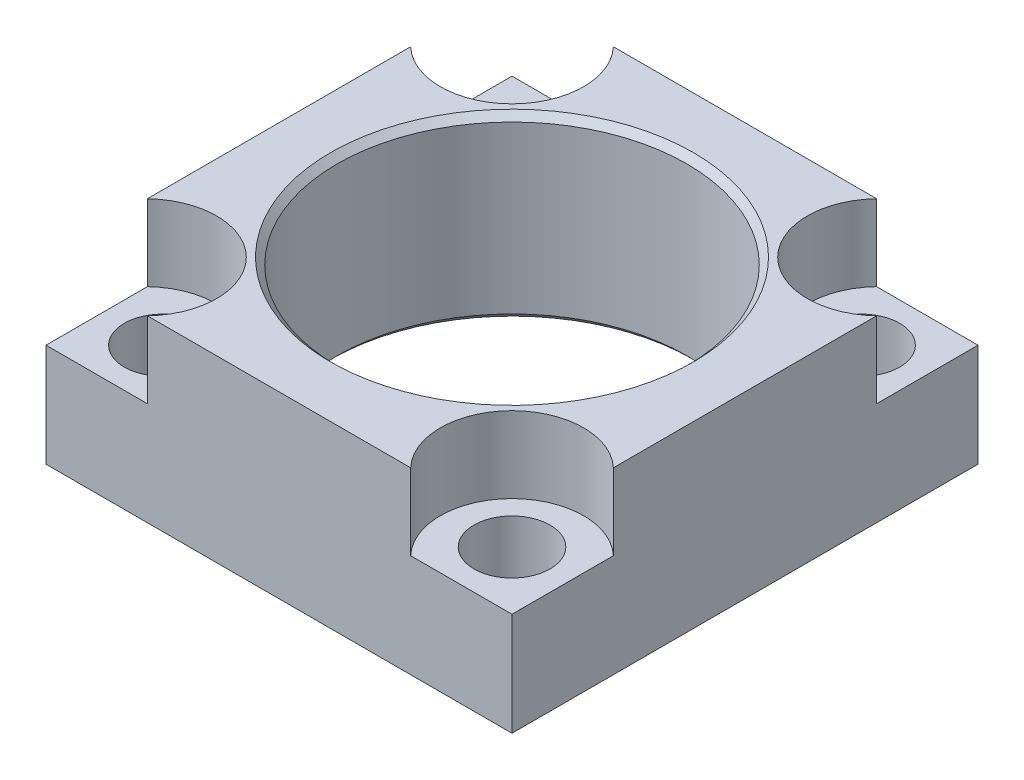
SolidWorks part; units mm, degrees
material "Alloy Steel"
ref_plane "Front Plane" through (0, 0, 0) normal (0, 0, 1) x (1, 0, 0)
ref_plane "Top Plane" through (0, 0, 0) normal (0, 1, 0) x (1, 0, 0)
ref_plane "Right Plane" through (0, 0, 0) normal (1, 0, 0) x (0, 0, -1)
sketch "Sketch1" plane through (0, 0, 0) normal (0, 1, 0) x (1, 0, 0)
  line L0 (41.275, 41.275) -> (-41.275, -41.275) construction
  line L1 (-41.275, 41.275) -> (41.275, 41.275)
  line L2 (-41.275, 41.275) -> (-41.275, -41.275)
  line L3 (-41.275, -41.275) -> (41.275, -41.275)
  line L4 (41.275, 41.275) -> (41.275, -41.275)
  line L5 (-41.275, 41.275) -> (41.275, -41.275) construction
  circle A0 centre (0, 0) radius 30.9753
  dimension "D3" = 61.9506
  dimension "D1" = 82.55
  dimension "D2" = 82.55
extrude "Extrude1" add sketch "Sketch1" along normal blind 31.75
sketch "Sketch2" plane through (0, 31.75, 0) normal (0, 1, 0) x (1, 0, 0)
  line L0 (-41.275, -41.275) -> (41.275, -41.275) construction
  line L1 (41.275, -41.275) -> (41.275, 41.275) construction
  line L2 (23.3196, -41.275) -> (41.275, -41.275)
  line L3 (41.275, -41.275) -> (41.275, -23.3196)
  line L4 (0, 0) -> (-25.3528, 0) construction
  line L5 (0, 0) -> (0, 27.5861) construction
  line L6 (41.275, 41.275) -> (41.275, 23.3196)
  line L7 (23.3196, 41.275) -> (41.275, 41.275)
  line L8 (-23.3196, 41.275) -> (-41.275, 41.275)
  line L9 (-41.275, 41.275) -> (-41.275, 23.3196)
  line L10 (-41.275, -41.275) -> (-41.275, -23.3196)
  line L11 (-23.3196, -41.275) -> (-41.275, -41.275)
  arc A0 (41.275, -23.3196) -> (23.3196, -41.275) centre (32.512, -32.512) ccw
  arc A1 (41.275, 23.3196) -> (23.3196, 41.275) centre (32.512, 32.512) cw
  arc A2 (-41.275, 23.3196) -> (-23.3196, 41.275) centre (-32.512, 32.512) ccw
  arc A3 (-41.275, -23.3196) -> (-23.3196, -41.275) centre (-32.512, -32.512) cw
  dimension "D1" = 12.7
  dimension "D2" = 32.512
  dimension "D3" = 32.512
extrude "Cut-Extrude1" cut sketch "Sketch2" against normal blind 13.4874
hole_wizard "Hole1" positions "Sketch4" profile "Sketch3" legacy end condition up to next
sketch "Sketch4" plane through (0, 18.2626, 0) normal (0, 1, 0) x (-1, 0, 0)
  point P0 (30.9626, 30.9626)
  point P6 (30.9626, -30.9626)
  point P9 (-30.9626, 30.9626)
  point P11 (-30.9626, -30.9626)
  dimension "D1" = 30.9626
  dimension "D2" = 30.9626
  dimension "D3" = 61.9252
  dimension "D4" = 61.9252
sketch "Sketch3" plane through (-30.9626, 18.2626, 30.9626) normal (1, 0, 0) x (0, 0, 1)
  line L0 (0, 0) -> (0, 18.2626)
  line L1 (0, 18.2626) -> (6.7437, 18.2626)
  line L2 (6.7437, 18.2626) -> (6.7437, 0)
  line L3 (6.7437, 0) -> (0, 0)
  line L4 (0, 110) -> (0, -10) construction
  dimension "Diameter" = 13.4874
  dimension "Depth" = 18.2626
sketch "Sketch5" plane through (0, 0, 0) normal (1, 0, 0) x (0, 0, -1)
  line L0 (0, 0) -> (0, 13.7269) construction
  line L1 (-22.3145, 15.875) -> (-9.8575, 15.875) construction
  line L2 (-19.812, 31.75) -> (-41.275, 31.75) construction
  line L3 (-41.275, 0) -> (41.275, 0) construction
  line L4 (-32.131, 31.75) -> (-30.9753, 31.75)
  line L5 (-30.9753, 31.75) -> (-30.9753, 30.5943)
  line L6 (-30.9753, 31.75) -> (-30.9753, 0) construction
  line L7 (-30.9753, 30.5943) -> (-32.131, 31.75)
  line L8 (-30.9753, 1.1557) -> (-32.131, 0)
  line L9 (-30.9753, 0) -> (-30.9753, 1.1557)
  line L10 (-32.131, 0) -> (-30.9753, 0)
  dimension "D1" = 45
  dimension "D2" = 64.262
revolve "Cut-Revolve1" cut sketch "Sketch5" angle 360 about L0
